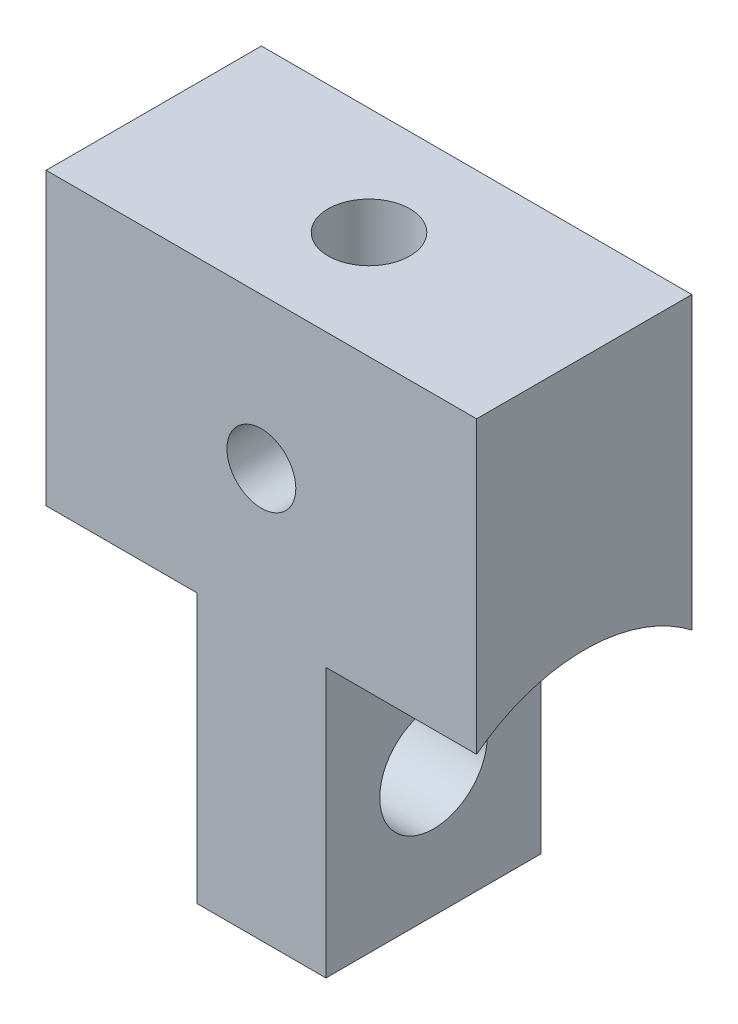
SolidWorks part; units mm, degrees
ref_plane "Front" through (0, 0, 0) normal (0, 0, 1) x (1, 0, 0)
ref_plane "Top" through (0, 0, 0) normal (0, 1, 0) x (1, 0, 0)
ref_plane "Right" through (0, 0, 0) normal (1, 0, 0) x (0, 0, -1)
sketch "Sketch1" plane through (0, 0, 0) normal (0, 0, 1) x (1, 0, 0)
  line L0 (0, 6.5) -> (0, -6.5) construction
  line L1 (-5, -6.5) -> (5, -6.5)
  line L2 (-5, -6.5) -> (-5, 6.5)
  line L3 (-5, 6.5) -> (5, 6.5)
  line L4 (5, -6.5) -> (5, 6.5)
  line L5 (-5, -6.5) -> (5, 6.5) construction
  line L6 (-5, 6.5) -> (5, -6.5) construction
  circle A0 centre (0, 3) radius 0.8
  point P0 (0, 0)
  dimension "D3" = 1.6
  dimension "D1" = 10
  dimension "D2" = 13
  dimension "D5" = 3.5
extrude "Boss-Extrude1" add sketch "Sketch1" along normal blind 5
sketch "Sketch3" plane through (-5, 0, 0) normal (-1, 0, 0) x (0, 0, 1)
  line L0 (2.5, -6.5) -> (2.5, -3.5) construction
  line L1 (5, -6.5) -> (0, -6.5) construction
  line L2 (-1.6, -3.5) -> (-1.6, -7.6)
  line L3 (-1.6, -7.6) -> (6.6, -7.6)
  line L4 (6.6, -7.6) -> (6.6, -3.5)
  arc A0 (6.6, -3.5) -> (-1.6, -3.5) centre (2.5, -3.5) ccw
  dimension "D2" = 8.2
  dimension "D1" = 3
extrude "Cut-Extrude2" cut sketch "Sketch3" against normal offset from surface (3.5 mm away) 1.5 up to plane "Right"
mirror "Mirror1" about plane through (0, 0, 0) normal (1, 0, 0) of "Cut-Extrude2"
sketch "Sketch4" plane through (-1.5, 0, 0) normal (-1, 0, 0) x (0, 0, 1)
  circle A0 centre (2.5, -3.5) radius 1.25
  dimension "D1" = 2.5
extrude "Cut-Extrude3" cut sketch "Sketch4" against normal through all
sketch "Sketch5" plane through (0, 6.5, 0) normal (0, 1, 0) x (1, 0, 0)
  line L0 (0, 0) -> (0, -5) construction
  line L1 (5, -5) -> (-5, -5) construction
  circle A0 centre (0, -2.5) radius 0.95
  dimension "D2" = 1.9
extrude "Cut-Extrude4" cut sketch "Sketch5" against normal blind 3
